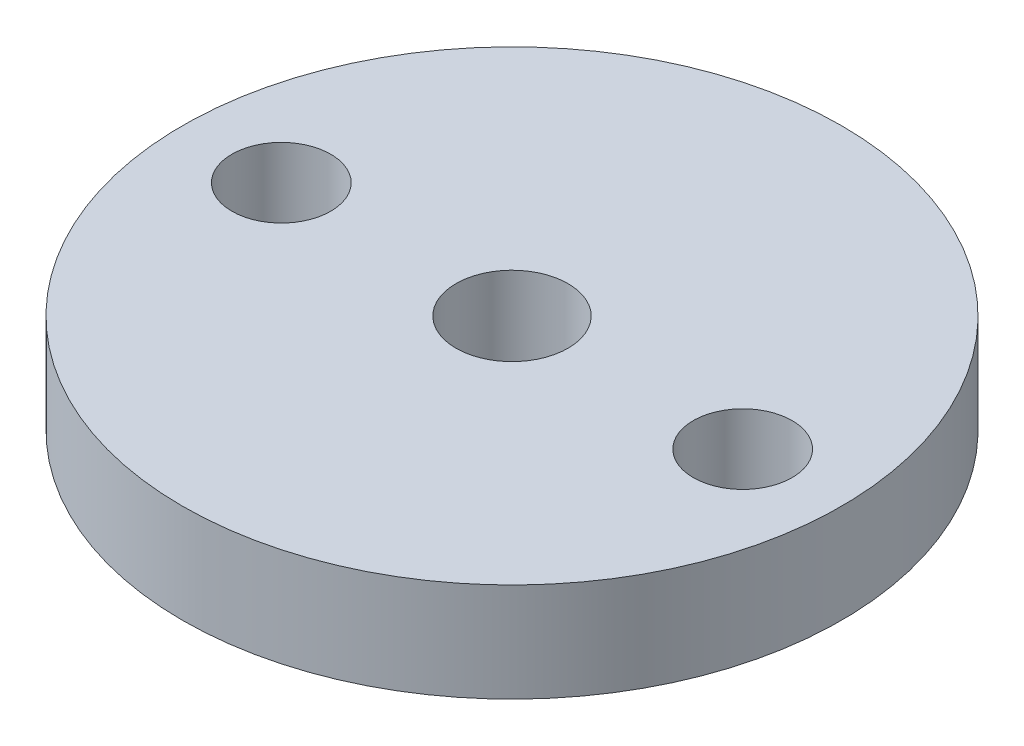
SolidWorks part; units mm, degrees
ref_plane "Front Plane" through (0, 0, 0) normal (0, 0, 1) x (1, 0, 0)
ref_plane "Top Plane" through (0, 0, 0) normal (0, 1, 0) x (1, 0, 0)
ref_plane "Right Plane" through (0, 0, 0) normal (1, 0, 0) x (0, 0, -1)
sketch "Croquis1" plane through (0, 0, 0) normal (0, 1, 0) x (1, 0, 0)
  circle A0 centre (0, 0) radius 10
  circle A1 centre (0, 0) radius 1.7
  circle A2 centre (7, 0) radius 1.5
  circle A3 centre (-7, 0) radius 1.5
  dimension "D1" = 3.4
  dimension "D2" = 20
  dimension "D5" = 3
  dimension "D3" = 7
  dimension "D4" = 7
extrude "Saliente-Extruir1" add sketch "Croquis1" along normal blind 3
